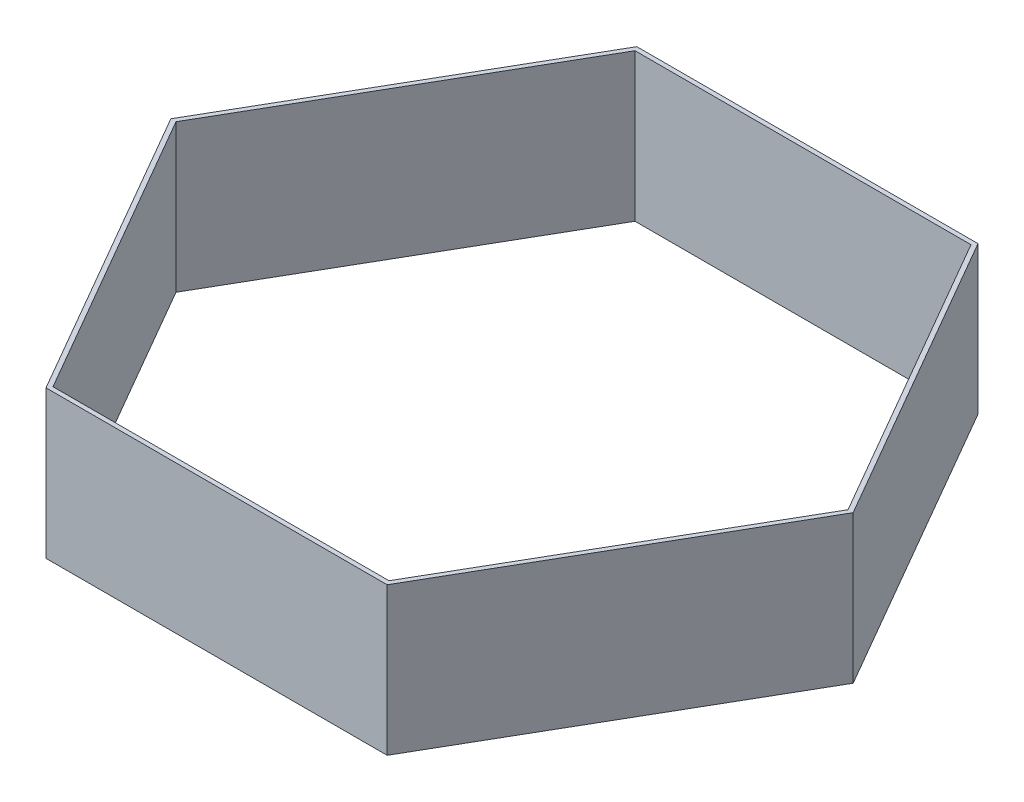
SolidWorks part; units mm, degrees
material "Thornel Mat VMA"
ref_plane "Alzado" through (0, 0, 0) normal (0, 0, 1) x (1, 0, 0)
ref_plane "Planta" through (0, 0, 0) normal (0, 1, 0) x (1, 0, 0)
ref_plane "Vista lateral" through (0, 0, 0) normal (1, 0, 0) x (0, 0, -1)
sketch "Croquis1" plane through (0, 0, 0) normal (0, 1, 0) x (1, 0, 0)
  line L1 (-115.4701, -200) -> (115.4701, -200)
  line L2 (115.4701, -200) -> (230.9401, 0)
  line L3 (230.9401, 0) -> (115.4701, 200)
  line L4 (115.4701, 200) -> (-115.4701, 200)
  line L5 (-115.4701, 200) -> (-230.9401, 0)
  line L6 (-230.9401, 0) -> (-115.4701, -200)
  line L7 (113.738, -197) -> (227.476, 0)
  line L8 (227.476, 0) -> (113.738, 197)
  line L9 (113.738, 197) -> (-113.738, 197)
  line L10 (-113.738, 197) -> (-227.476, 0)
  line L11 (-227.476, 0) -> (-113.738, -197)
  line L12 (-113.738, -197) -> (113.738, -197)
  circle A0 centre (0, 0) radius 200 construction
  circle A1 centre (0, 0) radius 197 construction
  dimension "D1" = 400
  dimension "D2" = 3
extrude "Saliente-Extruir1" add sketch "Croquis1" along normal blind 100
